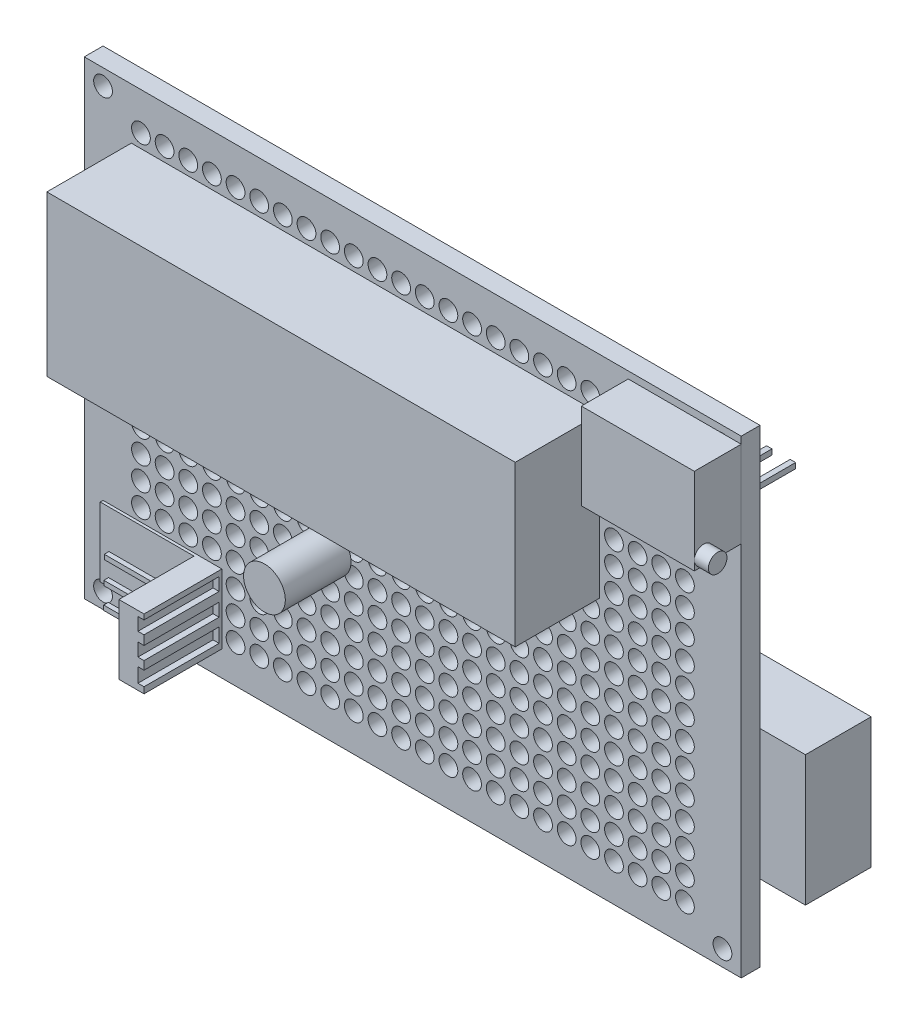
SolidWorks part; units mm, degrees
ref_plane "前视基准面" through (0, 0, 0) normal (0, 0, 1) x (1, 0, 0)
ref_plane "上视基准面" through (0, 0, 0) normal (0, 1, 0) x (1, 0, 0)
ref_plane "右视基准面" through (0, 0, 0) normal (1, 0, 0) x (0, 0, -1)
sketch "草图1" plane through (0, 0, 0) normal (0, 0, 1) x (1, 0, 0)
  line L1 (-36.6719, 23.0469) -> (33.3281, 23.0469)
  line L2 (-36.6719, 23.0469) -> (-36.6719, -26.9531)
  line L3 (-36.6719, -26.9531) -> (33.3281, -26.9531)
  line L4 (33.3281, 23.0469) -> (33.3281, -26.9531)
  circle A0 centre (31.3281, 21.3469) radius 1
  circle A1 centre (-34.6719, -25.2531) radius 1
  circle A2 centre (-34.6719, 21.3469) radius 1
  circle A3 centre (31.3281, -25.2531) radius 1
extrude "凸台-拉伸1" add sketch "草图1" along normal blind 2
sketch "草图2" plane through (0, 0, 0) normal (0, 0, -1) x (-1, 0, 0)
  circle A0 centre (-27.3281, 19.0469) radius 1
  circle A1 centre (-24.8081, 19.0469) radius 1
  circle A2 centre (-22.2881, 19.0469) radius 1
  circle A3 centre (-19.7681, 19.0469) radius 1
  circle A4 centre (-17.2481, 19.0469) radius 1
  circle A5 centre (-14.7281, 19.0469) radius 1
  circle A6 centre (-12.2081, 19.0469) radius 1
  circle A7 centre (-9.6881, 19.0469) radius 1
  circle A8 centre (-7.1681, 19.0469) radius 1
  circle A9 centre (-4.6481, 19.0469) radius 1
  circle A10 centre (-2.1281, 19.0469) radius 1
  circle A11 centre (0.3919, 19.0469) radius 1
  circle A12 centre (2.9119, 19.0469) radius 1
  circle A13 centre (5.4319, 19.0469) radius 1
  circle A14 centre (7.9519, 19.0469) radius 1
  circle A15 centre (10.4719, 19.0469) radius 1
  circle A16 centre (12.9919, 19.0469) radius 1
  circle A17 centre (15.5119, 19.0469) radius 1
  circle A18 centre (18.0319, 19.0469) radius 1
  circle A19 centre (20.5519, 19.0469) radius 1
  circle A20 centre (23.0719, 19.0469) radius 1
  circle A21 centre (25.5919, 19.0469) radius 1
  circle A22 centre (28.1119, 19.0469) radius 1
  circle A23 centre (30.6319, 19.0469) radius 1
  circle A24 centre (-24.8081, 16.5769) radius 1
  circle A25 centre (-22.2881, 16.5769) radius 1
  circle A26 centre (-19.7681, 16.5769) radius 1
  circle A27 centre (-17.2481, 16.5769) radius 1
  circle A28 centre (-14.7281, 16.5769) radius 1
  circle A29 centre (-12.2081, 16.5769) radius 1
  circle A30 centre (-9.6881, 16.5769) radius 1
  circle A31 centre (-7.1681, 16.5769) radius 1
  circle A32 centre (-4.6481, 16.5769) radius 1
  circle A33 centre (-2.1281, 16.5769) radius 1
  circle A34 centre (0.3919, 16.5769) radius 1
  circle A35 centre (2.9119, 16.5769) radius 1
  circle A36 centre (5.4319, 16.5769) radius 1
  circle A37 centre (7.9519, 16.5769) radius 1
  circle A38 centre (10.4719, 16.5769) radius 1
  circle A39 centre (12.9919, 16.5769) radius 1
  circle A40 centre (15.5119, 16.5769) radius 1
  circle A41 centre (18.0319, 16.5769) radius 1
  circle A42 centre (20.5519, 16.5769) radius 1
  circle A43 centre (23.0719, 16.5769) radius 1
  circle A44 centre (25.5919, 16.5769) radius 1
  circle A45 centre (28.1119, 16.5769) radius 1
  circle A46 centre (30.6319, 16.5769) radius 1
  circle A47 centre (-24.8081, 14.1069) radius 1
  circle A48 centre (-22.2881, 14.1069) radius 1
  circle A49 centre (-19.7681, 14.1069) radius 1
  circle A50 centre (-17.2481, 14.1069) radius 1
  circle A51 centre (-14.7281, 14.1069) radius 1
  circle A52 centre (-12.2081, 14.1069) radius 1
  circle A53 centre (-9.6881, 14.1069) radius 1
  circle A54 centre (-7.1681, 14.1069) radius 1
  circle A55 centre (-4.6481, 14.1069) radius 1
  circle A56 centre (-2.1281, 14.1069) radius 1
  circle A57 centre (0.3919, 14.1069) radius 1
  circle A58 centre (2.9119, 14.1069) radius 1
  circle A59 centre (5.4319, 14.1069) radius 1
  circle A60 centre (7.9519, 14.1069) radius 1
  circle A61 centre (10.4719, 14.1069) radius 1
  circle A62 centre (12.9919, 14.1069) radius 1
  circle A63 centre (15.5119, 14.1069) radius 1
  circle A64 centre (18.0319, 14.1069) radius 1
  circle A65 centre (20.5519, 14.1069) radius 1
  circle A66 centre (23.0719, 14.1069) radius 1
  circle A67 centre (25.5919, 14.1069) radius 1
  circle A68 centre (28.1119, 14.1069) radius 1
  circle A69 centre (30.6319, 14.1069) radius 1
  circle A70 centre (-24.8081, 11.6369) radius 1
  circle A71 centre (-22.2881, 11.6369) radius 1
  circle A72 centre (-19.7681, 11.6369) radius 1
  circle A73 centre (-17.2481, 11.6369) radius 1
  circle A74 centre (-14.7281, 11.6369) radius 1
  circle A75 centre (-12.2081, 11.6369) radius 1
  circle A76 centre (-9.6881, 11.6369) radius 1
  circle A77 centre (-7.1681, 11.6369) radius 1
  circle A78 centre (-4.6481, 11.6369) radius 1
  circle A79 centre (-2.1281, 11.6369) radius 1
  circle A80 centre (0.3919, 11.6369) radius 1
  circle A81 centre (2.9119, 11.6369) radius 1
  circle A82 centre (5.4319, 11.6369) radius 1
  circle A83 centre (7.9519, 11.6369) radius 1
  circle A84 centre (10.4719, 11.6369) radius 1
  circle A85 centre (12.9919, 11.6369) radius 1
  circle A86 centre (15.5119, 11.6369) radius 1
  circle A87 centre (18.0319, 11.6369) radius 1
  circle A88 centre (20.5519, 11.6369) radius 1
  circle A89 centre (23.0719, 11.6369) radius 1
  circle A90 centre (25.5919, 11.6369) radius 1
  circle A91 centre (28.1119, 11.6369) radius 1
  circle A92 centre (30.6319, 11.6369) radius 1
  circle A93 centre (-24.8081, 9.1669) radius 1
  circle A94 centre (-22.2881, 9.1669) radius 1
  circle A95 centre (-19.7681, 9.1669) radius 1
  circle A96 centre (-17.2481, 9.1669) radius 1
  circle A97 centre (-14.7281, 9.1669) radius 1
  circle A98 centre (-12.2081, 9.1669) radius 1
  circle A99 centre (-9.6881, 9.1669) radius 1
  circle A100 centre (-7.1681, 9.1669) radius 1
  circle A101 centre (-4.6481, 9.1669) radius 1
  circle A102 centre (-2.1281, 9.1669) radius 1
  circle A103 centre (0.3919, 9.1669) radius 1
  circle A104 centre (2.9119, 9.1669) radius 1
  circle A105 centre (5.4319, 9.1669) radius 1
  circle A106 centre (7.9519, 9.1669) radius 1
  circle A107 centre (10.4719, 9.1669) radius 1
  circle A108 centre (12.9919, 9.1669) radius 1
  circle A109 centre (15.5119, 9.1669) radius 1
  circle A110 centre (18.0319, 9.1669) radius 1
  circle A111 centre (20.5519, 9.1669) radius 1
  circle A112 centre (23.0719, 9.1669) radius 1
  circle A113 centre (25.5919, 9.1669) radius 1
  circle A114 centre (28.1119, 9.1669) radius 1
  circle A115 centre (30.6319, 9.1669) radius 1
  circle A116 centre (-24.8081, 6.6969) radius 1
  circle A117 centre (-22.2881, 6.6969) radius 1
  circle A118 centre (-19.7681, 6.6969) radius 1
  circle A119 centre (-17.2481, 6.6969) radius 1
  circle A120 centre (-14.7281, 6.6969) radius 1
  circle A121 centre (-12.2081, 6.6969) radius 1
  circle A122 centre (-9.6881, 6.6969) radius 1
  circle A123 centre (-7.1681, 6.6969) radius 1
  circle A124 centre (-4.6481, 6.6969) radius 1
  circle A125 centre (-2.1281, 6.6969) radius 1
  circle A126 centre (0.3919, 6.6969) radius 1
  circle A127 centre (2.9119, 6.6969) radius 1
  circle A128 centre (5.4319, 6.6969) radius 1
  circle A129 centre (7.9519, 6.6969) radius 1
  circle A130 centre (10.4719, 6.6969) radius 1
  circle A131 centre (12.9919, 6.6969) radius 1
  circle A132 centre (15.5119, 6.6969) radius 1
  circle A133 centre (18.0319, 6.6969) radius 1
  circle A134 centre (20.5519, 6.6969) radius 1
  circle A135 centre (23.0719, 6.6969) radius 1
  circle A136 centre (25.5919, 6.6969) radius 1
  circle A137 centre (28.1119, 6.6969) radius 1
  circle A138 centre (30.6319, 6.6969) radius 1
  circle A139 centre (-24.8081, 4.2269) radius 1
  circle A140 centre (-22.2881, 4.2269) radius 1
  circle A141 centre (-19.7681, 4.2269) radius 1
  circle A142 centre (-17.2481, 4.2269) radius 1
  circle A143 centre (-14.7281, 4.2269) radius 1
  circle A144 centre (-12.2081, 4.2269) radius 1
  circle A145 centre (-9.6881, 4.2269) radius 1
  circle A146 centre (-7.1681, 4.2269) radius 1
  circle A147 centre (-4.6481, 4.2269) radius 1
  circle A148 centre (-2.1281, 4.2269) radius 1
  circle A149 centre (0.3919, 4.2269) radius 1
  circle A150 centre (2.9119, 4.2269) radius 1
  circle A151 centre (5.4319, 4.2269) radius 1
  circle A152 centre (7.9519, 4.2269) radius 1
  circle A153 centre (10.4719, 4.2269) radius 1
  circle A154 centre (12.9919, 4.2269) radius 1
  circle A155 centre (15.5119, 4.2269) radius 1
  circle A156 centre (18.0319, 4.2269) radius 1
  circle A157 centre (20.5519, 4.2269) radius 1
  circle A158 centre (23.0719, 4.2269) radius 1
  circle A159 centre (25.5919, 4.2269) radius 1
  circle A160 centre (28.1119, 4.2269) radius 1
  circle A161 centre (30.6319, 4.2269) radius 1
  circle A162 centre (-24.8081, 1.7569) radius 1
  circle A163 centre (-22.2881, 1.7569) radius 1
  circle A164 centre (-19.7681, 1.7569) radius 1
  circle A165 centre (-17.2481, 1.7569) radius 1
  circle A166 centre (-14.7281, 1.7569) radius 1
  circle A167 centre (-12.2081, 1.7569) radius 1
  circle A168 centre (-9.6881, 1.7569) radius 1
  circle A169 centre (-7.1681, 1.7569) radius 1
  circle A170 centre (-4.6481, 1.7569) radius 1
  circle A171 centre (-2.1281, 1.7569) radius 1
  circle A172 centre (0.3919, 1.7569) radius 1
  circle A173 centre (2.9119, 1.7569) radius 1
  circle A174 centre (5.4319, 1.7569) radius 1
  circle A175 centre (7.9519, 1.7569) radius 1
  circle A176 centre (10.4719, 1.7569) radius 1
  circle A177 centre (12.9919, 1.7569) radius 1
  circle A178 centre (15.5119, 1.7569) radius 1
  circle A179 centre (18.0319, 1.7569) radius 1
  circle A180 centre (20.5519, 1.7569) radius 1
  circle A181 centre (23.0719, 1.7569) radius 1
  circle A182 centre (25.5919, 1.7569) radius 1
  circle A183 centre (28.1119, 1.7569) radius 1
  circle A184 centre (30.6319, 1.7569) radius 1
  circle A185 centre (-24.8081, -0.7131) radius 1
  circle A186 centre (-22.2881, -0.7131) radius 1
  circle A187 centre (-19.7681, -0.7131) radius 1
  circle A188 centre (-17.2481, -0.7131) radius 1
  circle A189 centre (-14.7281, -0.7131) radius 1
  circle A190 centre (-12.2081, -0.7131) radius 1
  circle A191 centre (-9.6881, -0.7131) radius 1
  circle A192 centre (-7.1681, -0.7131) radius 1
  circle A193 centre (-4.6481, -0.7131) radius 1
  circle A194 centre (-2.1281, -0.7131) radius 1
  circle A195 centre (0.3919, -0.7131) radius 1
  circle A196 centre (2.9119, -0.7131) radius 1
  circle A197 centre (5.4319, -0.7131) radius 1
  circle A198 centre (7.9519, -0.7131) radius 1
  circle A199 centre (10.4719, -0.7131) radius 1
  circle A200 centre (12.9919, -0.7131) radius 1
  circle A201 centre (15.5119, -0.7131) radius 1
  circle A202 centre (18.0319, -0.7131) radius 1
  circle A203 centre (20.5519, -0.7131) radius 1
  circle A204 centre (23.0719, -0.7131) radius 1
  circle A205 centre (25.5919, -0.7131) radius 1
  circle A206 centre (28.1119, -0.7131) radius 1
  circle A207 centre (30.6319, -0.7131) radius 1
  circle A208 centre (-24.8081, -3.1831) radius 1
  circle A209 centre (-22.2881, -3.1831) radius 1
  circle A210 centre (-19.7681, -3.1831) radius 1
  circle A211 centre (-17.2481, -3.1831) radius 1
  circle A212 centre (-14.7281, -3.1831) radius 1
  circle A213 centre (-12.2081, -3.1831) radius 1
  circle A214 centre (-9.6881, -3.1831) radius 1
  circle A215 centre (-7.1681, -3.1831) radius 1
  circle A216 centre (-4.6481, -3.1831) radius 1
  circle A217 centre (-2.1281, -3.1831) radius 1
  circle A218 centre (0.3919, -3.1831) radius 1
  circle A219 centre (2.9119, -3.1831) radius 1
  circle A220 centre (5.4319, -3.1831) radius 1
  circle A221 centre (7.9519, -3.1831) radius 1
  circle A222 centre (10.4719, -3.1831) radius 1
  circle A223 centre (12.9919, -3.1831) radius 1
  circle A224 centre (15.5119, -3.1831) radius 1
  circle A225 centre (18.0319, -3.1831) radius 1
  circle A226 centre (20.5519, -3.1831) radius 1
  circle A227 centre (23.0719, -3.1831) radius 1
  circle A228 centre (25.5919, -3.1831) radius 1
  circle A229 centre (28.1119, -3.1831) radius 1
  circle A230 centre (30.6319, -3.1831) radius 1
  circle A231 centre (-24.8081, -5.6531) radius 1
  circle A232 centre (-22.2881, -5.6531) radius 1
  circle A233 centre (-19.7681, -5.6531) radius 1
  circle A234 centre (-17.2481, -5.6531) radius 1
  circle A235 centre (-14.7281, -5.6531) radius 1
  circle A236 centre (-12.2081, -5.6531) radius 1
  circle A237 centre (-9.6881, -5.6531) radius 1
  circle A238 centre (-7.1681, -5.6531) radius 1
  circle A239 centre (-4.6481, -5.6531) radius 1
  circle A240 centre (-2.1281, -5.6531) radius 1
  circle A241 centre (0.3919, -5.6531) radius 1
  circle A242 centre (2.9119, -5.6531) radius 1
  circle A243 centre (5.4319, -5.6531) radius 1
  circle A244 centre (7.9519, -5.6531) radius 1
  circle A245 centre (10.4719, -5.6531) radius 1
  circle A246 centre (12.9919, -5.6531) radius 1
  circle A247 centre (15.5119, -5.6531) radius 1
  circle A248 centre (18.0319, -5.6531) radius 1
  circle A249 centre (20.5519, -5.6531) radius 1
  circle A250 centre (23.0719, -5.6531) radius 1
  circle A251 centre (25.5919, -5.6531) radius 1
  circle A252 centre (28.1119, -5.6531) radius 1
  circle A253 centre (30.6319, -5.6531) radius 1
  circle A254 centre (-24.8081, -8.1231) radius 1
  circle A255 centre (-22.2881, -8.1231) radius 1
  circle A256 centre (-19.7681, -8.1231) radius 1
  circle A257 centre (-17.2481, -8.1231) radius 1
  circle A258 centre (-14.7281, -8.1231) radius 1
  circle A259 centre (-12.2081, -8.1231) radius 1
  circle A260 centre (-9.6881, -8.1231) radius 1
  circle A261 centre (-7.1681, -8.1231) radius 1
  circle A262 centre (-4.6481, -8.1231) radius 1
  circle A263 centre (-2.1281, -8.1231) radius 1
  circle A264 centre (0.3919, -8.1231) radius 1
  circle A265 centre (2.9119, -8.1231) radius 1
  circle A266 centre (5.4319, -8.1231) radius 1
  circle A267 centre (7.9519, -8.1231) radius 1
  circle A268 centre (10.4719, -8.1231) radius 1
  circle A269 centre (12.9919, -8.1231) radius 1
  circle A270 centre (15.5119, -8.1231) radius 1
  circle A271 centre (18.0319, -8.1231) radius 1
  circle A272 centre (20.5519, -8.1231) radius 1
  circle A273 centre (23.0719, -8.1231) radius 1
  circle A274 centre (25.5919, -8.1231) radius 1
  circle A275 centre (28.1119, -8.1231) radius 1
  circle A276 centre (30.6319, -8.1231) radius 1
  circle A277 centre (-24.8081, -10.5931) radius 1
  circle A278 centre (-22.2881, -10.5931) radius 1
  circle A279 centre (-19.7681, -10.5931) radius 1
  circle A280 centre (-17.2481, -10.5931) radius 1
  circle A281 centre (-14.7281, -10.5931) radius 1
  circle A282 centre (-12.2081, -10.5931) radius 1
  circle A283 centre (-9.6881, -10.5931) radius 1
  circle A284 centre (-7.1681, -10.5931) radius 1
  circle A285 centre (-4.6481, -10.5931) radius 1
  circle A286 centre (-2.1281, -10.5931) radius 1
  circle A287 centre (0.3919, -10.5931) radius 1
  circle A288 centre (2.9119, -10.5931) radius 1
  circle A289 centre (5.4319, -10.5931) radius 1
  circle A290 centre (7.9519, -10.5931) radius 1
  circle A291 centre (10.4719, -10.5931) radius 1
  circle A292 centre (12.9919, -10.5931) radius 1
  circle A293 centre (15.5119, -10.5931) radius 1
  circle A294 centre (18.0319, -10.5931) radius 1
  circle A295 centre (20.5519, -10.5931) radius 1
  circle A296 centre (23.0719, -10.5931) radius 1
  circle A297 centre (25.5919, -10.5931) radius 1
  circle A298 centre (28.1119, -10.5931) radius 1
  circle A299 centre (30.6319, -10.5931) radius 1
  circle A300 centre (-24.8081, -13.0631) radius 1
  circle A301 centre (-22.2881, -13.0631) radius 1
  circle A302 centre (-19.7681, -13.0631) radius 1
  circle A303 centre (-17.2481, -13.0631) radius 1
  circle A304 centre (-14.7281, -13.0631) radius 1
  circle A305 centre (-12.2081, -13.0631) radius 1
  circle A306 centre (-9.6881, -13.0631) radius 1
  circle A307 centre (-7.1681, -13.0631) radius 1
  circle A308 centre (-4.6481, -13.0631) radius 1
  circle A309 centre (-2.1281, -13.0631) radius 1
  circle A310 centre (0.3919, -13.0631) radius 1
  circle A311 centre (2.9119, -13.0631) radius 1
  circle A312 centre (5.4319, -13.0631) radius 1
  circle A313 centre (7.9519, -13.0631) radius 1
  circle A314 centre (10.4719, -13.0631) radius 1
  circle A315 centre (12.9919, -13.0631) radius 1
  circle A316 centre (15.5119, -13.0631) radius 1
  circle A317 centre (18.0319, -13.0631) radius 1
  circle A318 centre (20.5519, -13.0631) radius 1
  circle A319 centre (23.0719, -13.0631) radius 1
  circle A320 centre (25.5919, -13.0631) radius 1
  circle A321 centre (28.1119, -13.0631) radius 1
  circle A322 centre (30.6319, -13.0631) radius 1
  circle A323 centre (-24.8081, -15.5331) radius 1
  circle A324 centre (-22.2881, -15.5331) radius 1
  circle A325 centre (-19.7681, -15.5331) radius 1
  circle A326 centre (-17.2481, -15.5331) radius 1
  circle A327 centre (-14.7281, -15.5331) radius 1
  circle A328 centre (-12.2081, -15.5331) radius 1
  circle A329 centre (-9.6881, -15.5331) radius 1
  circle A330 centre (-7.1681, -15.5331) radius 1
  circle A331 centre (-4.6481, -15.5331) radius 1
  circle A332 centre (-2.1281, -15.5331) radius 1
  circle A333 centre (0.3919, -15.5331) radius 1
  circle A334 centre (2.9119, -15.5331) radius 1
  circle A335 centre (5.4319, -15.5331) radius 1
  circle A336 centre (7.9519, -15.5331) radius 1
  circle A337 centre (10.4719, -15.5331) radius 1
  circle A338 centre (12.9919, -15.5331) radius 1
  circle A339 centre (15.5119, -15.5331) radius 1
  circle A340 centre (18.0319, -15.5331) radius 1
  circle A341 centre (20.5519, -15.5331) radius 1
  circle A342 centre (23.0719, -15.5331) radius 1
  circle A343 centre (25.5919, -15.5331) radius 1
  circle A344 centre (28.1119, -15.5331) radius 1
  circle A345 centre (30.6319, -15.5331) radius 1
  circle A346 centre (-24.8081, -18.0031) radius 1
  circle A347 centre (-22.2881, -18.0031) radius 1
  circle A348 centre (-19.7681, -18.0031) radius 1
  circle A349 centre (-17.2481, -18.0031) radius 1
  circle A350 centre (-14.7281, -18.0031) radius 1
  circle A351 centre (-12.2081, -18.0031) radius 1
  circle A352 centre (-9.6881, -18.0031) radius 1
  circle A353 centre (-7.1681, -18.0031) radius 1
  circle A354 centre (-4.6481, -18.0031) radius 1
  circle A355 centre (-2.1281, -18.0031) radius 1
  circle A356 centre (0.3919, -18.0031) radius 1
  circle A357 centre (2.9119, -18.0031) radius 1
  circle A358 centre (5.4319, -18.0031) radius 1
  circle A359 centre (7.9519, -18.0031) radius 1
  circle A360 centre (10.4719, -18.0031) radius 1
  circle A361 centre (12.9919, -18.0031) radius 1
  circle A362 centre (15.5119, -18.0031) radius 1
  circle A363 centre (18.0319, -18.0031) radius 1
  circle A364 centre (20.5519, -18.0031) radius 1
  circle A365 centre (23.0719, -18.0031) radius 1
  circle A366 centre (25.5919, -18.0031) radius 1
  circle A367 centre (28.1119, -18.0031) radius 1
  circle A368 centre (30.6319, -18.0031) radius 1
  circle A369 centre (-24.8081, -20.4731) radius 1
  circle A370 centre (-22.2881, -20.4731) radius 1
  circle A371 centre (-19.7681, -20.4731) radius 1
  circle A372 centre (-17.2481, -20.4731) radius 1
  circle A373 centre (-14.7281, -20.4731) radius 1
  circle A374 centre (-12.2081, -20.4731) radius 1
  circle A375 centre (-9.6881, -20.4731) radius 1
  circle A376 centre (-7.1681, -20.4731) radius 1
  circle A377 centre (-4.6481, -20.4731) radius 1
  circle A378 centre (-2.1281, -20.4731) radius 1
  circle A379 centre (0.3919, -20.4731) radius 1
  circle A380 centre (2.9119, -20.4731) radius 1
  circle A381 centre (5.4319, -20.4731) radius 1
  circle A382 centre (7.9519, -20.4731) radius 1
  circle A383 centre (10.4719, -20.4731) radius 1
  circle A384 centre (12.9919, -20.4731) radius 1
  circle A385 centre (15.5119, -20.4731) radius 1
  circle A386 centre (18.0319, -20.4731) radius 1
  circle A387 centre (20.5519, -20.4731) radius 1
  circle A388 centre (23.0719, -20.4731) radius 1
  circle A389 centre (25.5919, -20.4731) radius 1
  circle A390 centre (28.1119, -20.4731) radius 1
  circle A391 centre (30.6319, -20.4731) radius 1
  circle A392 centre (-24.8081, -22.9431) radius 1
  circle A393 centre (-22.2881, -22.9431) radius 1
  circle A394 centre (-19.7681, -22.9431) radius 1
  circle A395 centre (-17.2481, -22.9431) radius 1
  circle A396 centre (-14.7281, -22.9431) radius 1
  circle A397 centre (-12.2081, -22.9431) radius 1
  circle A398 centre (-9.6881, -22.9431) radius 1
  circle A399 centre (-7.1681, -22.9431) radius 1
  circle A400 centre (-4.6481, -22.9431) radius 1
  circle A401 centre (-2.1281, -22.9431) radius 1
  circle A402 centre (0.3919, -22.9431) radius 1
  circle A403 centre (2.9119, -22.9431) radius 1
  circle A404 centre (5.4319, -22.9431) radius 1
  circle A405 centre (7.9519, -22.9431) radius 1
  circle A406 centre (10.4719, -22.9431) radius 1
  circle A407 centre (12.9919, -22.9431) radius 1
  circle A408 centre (15.5119, -22.9431) radius 1
  circle A409 centre (18.0319, -22.9431) radius 1
  circle A410 centre (20.5519, -22.9431) radius 1
  circle A411 centre (23.0719, -22.9431) radius 1
  circle A412 centre (25.5919, -22.9431) radius 1
  circle A413 centre (28.1119, -22.9431) radius 1
  circle A414 centre (30.6319, -22.9431) radius 1
  circle A415 centre (-27.3281, 16.5769) radius 1
  circle A416 centre (-27.3281, 14.1069) radius 1
  circle A417 centre (-27.3281, 11.6369) radius 1
  circle A418 centre (-27.3281, 9.1669) radius 1
  circle A419 centre (-27.3281, 6.6969) radius 1
  circle A420 centre (-27.3281, 4.2269) radius 1
  circle A421 centre (-27.3281, 1.7569) radius 1
  circle A422 centre (-27.3281, -0.7131) radius 1
  circle A423 centre (-27.3281, -3.1831) radius 1
  circle A424 centre (-27.3281, -5.6531) radius 1
  circle A425 centre (-27.3281, -8.1231) radius 1
  circle A426 centre (-27.3281, -10.5931) radius 1
  circle A427 centre (-27.3281, -13.0631) radius 1
  circle A428 centre (-27.3281, -15.5331) radius 1
  circle A429 centre (-27.3281, -18.0031) radius 1
  circle A430 centre (-27.3281, -20.4731) radius 1
  circle A431 centre (-27.3281, -22.9431) radius 1
  dimension "D1" = 24
  dimension "D2" = 18
extrude "切除-拉伸1" cut sketch "草图2" against normal blind 2
sketch "草图3" plane through (0, 0, 2) normal (0, 0, 1) x (1, 0, 0)
  line L1 (-31.656, 17.5923) -> (18.2481, 17.5923)
  line L2 (-31.656, 17.5923) -> (-31.656, 0.5632)
  line L3 (-31.656, 0.5632) -> (18.2481, 0.5632)
  line L4 (18.2481, 17.5923) -> (18.2481, 0.5632)
extrude "凸台-拉伸3" add sketch "草图3" along normal blind 9 separate body
sketch "草图4" plane through (0, 0, 2) normal (0, 0, 1) x (1, 0, 0)
  line L0 (33.3281, -26.9531) -> (33.3281, 23.0469) construction
  line L1 (33.3281, 22.3025) -> (21.2881, 22.3025)
  line L2 (33.3281, 22.3025) -> (33.3281, 13.1069)
  line L3 (33.3281, 13.1069) -> (21.2881, 13.1069)
  line L4 (21.2881, 22.3025) -> (21.2881, 13.1069)
extrude "凸台-拉伸4" add sketch "草图4" along normal blind 5 separate body
sketch "草图5" plane through (33.3281, 0, 0) normal (1, 0, 0) x (0, 0, -1)
  circle A0 centre (-6.0085, 14.0984) radius 0.9915
extrude "凸台-拉伸5" add sketch "草图5" along normal blind 1.5
sketch "草图6" plane through (0, 0, 2) normal (0, 0, 1) x (1, 0, 0)
  line L1 (-34.6719, -24.2531) -> (-22.0048, -24.2531)
  line L2 (-34.6719, -24.2531) -> (-34.6719, -16.8774)
  line L3 (-34.6719, -16.8774) -> (-22.0048, -16.8774)
  line L4 (-22.0048, -24.2531) -> (-22.0048, -16.8774)
  circle A0 centre (-34.6719, -25.2531) radius 1 construction
extrude "凸台-拉伸6" add sketch "草图6" along normal blind 0.3
sketch "草图7" plane through (0, 0, 2.3) normal (0, 0, 1) x (1, 0, 0)
  line L1 (-22.0048, -16.8774) -> (-34.6719, -16.8774) construction
  line L2 (-34.6719, -24.2531) -> (-22.0048, -24.2531) construction
  line L3 (-24.6793, -24.2531) -> (-22.0048, -24.2531)
  line L4 (-22.0048, -16.8774) -> (-22.0048, -17.4292)
  line L5 (-22.0048, -24.2531) -> (-22.0048, -16.8774) construction
  line L6 (-22.0048, -24.2531) -> (-22.0048, -16.8774) construction
  line L7 (-22.0048, -17.4292) -> (-22.6503, -17.4292)
  line L8 (-22.6503, -17.4292) -> (-22.6503, -18.8012)
  line L9 (-22.6503, -18.8012) -> (-22.0048, -18.8012)
  line L10 (-22.0048, -18.8012) -> (-22.0048, -19.7867)
  line L11 (-22.0048, -19.7867) -> (-22.6503, -19.7867)
  line L12 (-22.6503, -19.7867) -> (-22.6503, -21.1781)
  line L13 (-22.6503, -21.1781) -> (-22.0048, -21.1781)
  line L14 (-22.0048, -21.1781) -> (-22.0048, -22.067)
  line L15 (-22.0048, -22.067) -> (-22.6503, -22.067)
  line L16 (-22.6503, -22.067) -> (-22.6503, -23.5936)
  line L17 (-22.6503, -23.5936) -> (-22.0048, -23.5936)
  line L18 (-22.0048, -23.5936) -> (-22.0048, -24.2531)
  line L19 (-24.6793, -24.2531) -> (-24.6793, -16.8774)
  line L20 (-22.0048, -16.8774) -> (-24.6793, -16.8774)
extrude "凸台-拉伸7" add sketch "草图7" along normal blind 8
sketch "草图8" plane through (-22.6503, 0, 0) normal (1, 0, 0) x (0, 0, -1)
  line L0 (-5.9346, -20.2759) -> (-5.4346, -20.2759)
  line L1 (-5.8878, -17.8955) -> (-5.3878, -17.8955)
  line L2 (-5.8878, -17.8955) -> (-5.8878, -18.3955)
  line L3 (-5.8878, -18.3955) -> (-5.3878, -18.3955)
  line L4 (-5.3878, -17.8955) -> (-5.3878, -18.3955)
  line L5 (-5.9346, -20.2759) -> (-5.9346, -20.7759)
  line L6 (-5.9346, -20.7759) -> (-5.4346, -20.7759)
  line L7 (-5.4346, -20.2759) -> (-5.4346, -20.7759)
  line L8 (-5.9491, -22.5548) -> (-5.4491, -22.5548)
  line L9 (-5.9491, -22.5548) -> (-5.9491, -23.0548)
  line L10 (-5.9491, -23.0548) -> (-5.4491, -23.0548)
  line L11 (-5.4491, -22.5548) -> (-5.4491, -23.0548)
extrude "凸台-拉伸8" add sketch "草图8" against normal blind 8
sketch "草图9" plane through (0, 0, 2) normal (0, 0, 1) x (1, 0, 0)
  circle A1 centre (-10.4719, -9.3623) radius 2.2236
extrude "凸台-拉伸9" add sketch "草图9" along normal blind 7
sketch "草图10" plane through (0, 0, 0) normal (0, 0, -1) x (-1, 0, 0)
  line L1 (-38.1694, -4.9279) -> (-24.0487, -4.9279)
  line L2 (-38.1694, -4.9279) -> (-38.1694, -18.8132)
  line L3 (-38.1694, -18.8132) -> (-24.0487, -18.8132)
  line L4 (-24.0487, -4.9279) -> (-24.0487, -18.8132)
extrude "凸台-拉伸12" add sketch "草图10" along normal blind 7 separate body
sketch "草图12" plane through (0, 0, 0) normal (0, 0, -1) x (-1, 0, 0)
  line L1 (6.7255, 10.4406) -> (-28.7236, 10.4406)
  line L2 (6.7255, 10.4406) -> (6.7255, 12.9106)
  line L3 (6.7255, 12.9106) -> (-28.7236, 12.9106)
  line L4 (-28.7236, 10.4406) -> (-28.7236, 12.9106)
extrude "凸台-拉伸13" add sketch "草图12" along normal blind 2.5
sketch "草图13" plane through (0, 0, -2.5) normal (0, 0, -1) x (-1, 0, 0)
  line L0 (3.1925, 12.0124) -> (2.6154, 12.0124)
  line L1 (5.7125, 12.0124) -> (5.1354, 12.0124)
  line L2 (5.7125, 12.0124) -> (5.7125, 11.4352)
  line L3 (5.7125, 11.4352) -> (5.1354, 11.4352)
  line L4 (5.1354, 12.0124) -> (5.1354, 11.4352)
  line L5 (3.1925, 12.0124) -> (3.1925, 11.4352)
  line L6 (3.1925, 11.4352) -> (2.6154, 11.4352)
  line L7 (2.6154, 12.0124) -> (2.6154, 11.4352)
  line L8 (0.6725, 12.0124) -> (0.0954, 12.0124)
  line L9 (0.6725, 12.0124) -> (0.6725, 11.4352)
  line L10 (0.6725, 11.4352) -> (0.0954, 11.4352)
  line L11 (0.0954, 12.0124) -> (0.0954, 11.4352)
  line L12 (-1.8475, 12.0124) -> (-2.4246, 12.0124)
  line L13 (-1.8475, 12.0124) -> (-1.8475, 11.4352)
  line L14 (-1.8475, 11.4352) -> (-2.4246, 11.4352)
  line L15 (-2.4246, 12.0124) -> (-2.4246, 11.4352)
  line L16 (-4.3675, 12.0124) -> (-4.9446, 12.0124)
  line L17 (-4.3675, 12.0124) -> (-4.3675, 11.4352)
  line L18 (-4.3675, 11.4352) -> (-4.9446, 11.4352)
  line L19 (-4.9446, 12.0124) -> (-4.9446, 11.4352)
  line L20 (-6.8875, 12.0124) -> (-7.4646, 12.0124)
  line L21 (-6.8875, 12.0124) -> (-6.8875, 11.4352)
  line L22 (-6.8875, 11.4352) -> (-7.4646, 11.4352)
  line L23 (-7.4646, 12.0124) -> (-7.4646, 11.4352)
  line L24 (-9.4075, 12.0124) -> (-9.9846, 12.0124)
  line L25 (-9.4075, 12.0124) -> (-9.4075, 11.4352)
  line L26 (-9.4075, 11.4352) -> (-9.9846, 11.4352)
  line L27 (-9.9846, 12.0124) -> (-9.9846, 11.4352)
  line L28 (-11.9275, 12.0124) -> (-12.5046, 12.0124)
  line L29 (-11.9275, 12.0124) -> (-11.9275, 11.4352)
  line L30 (-11.9275, 11.4352) -> (-12.5046, 11.4352)
  line L31 (-12.5046, 12.0124) -> (-12.5046, 11.4352)
  line L32 (-14.4475, 12.0124) -> (-15.0246, 12.0124)
  line L33 (-14.4475, 12.0124) -> (-14.4475, 11.4352)
  line L34 (-14.4475, 11.4352) -> (-15.0246, 11.4352)
  line L35 (-15.0246, 12.0124) -> (-15.0246, 11.4352)
  line L36 (-16.9675, 12.0124) -> (-17.5446, 12.0124)
  line L37 (-16.9675, 12.0124) -> (-16.9675, 11.4352)
  line L38 (-16.9675, 11.4352) -> (-17.5446, 11.4352)
  line L39 (-17.5446, 12.0124) -> (-17.5446, 11.4352)
  line L40 (-19.4875, 12.0124) -> (-20.0646, 12.0124)
  line L41 (-19.4875, 12.0124) -> (-19.4875, 11.4352)
  line L42 (-19.4875, 11.4352) -> (-20.0646, 11.4352)
  line L43 (-20.0646, 12.0124) -> (-20.0646, 11.4352)
  line L44 (-22.0075, 12.0124) -> (-22.5846, 12.0124)
  line L45 (-22.0075, 12.0124) -> (-22.0075, 11.4352)
  line L46 (-22.0075, 11.4352) -> (-22.5846, 11.4352)
  line L47 (-22.5846, 12.0124) -> (-22.5846, 11.4352)
  line L48 (-24.5275, 12.0124) -> (-25.1046, 12.0124)
  line L49 (-24.5275, 12.0124) -> (-24.5275, 11.4352)
  line L50 (-24.5275, 11.4352) -> (-25.1046, 11.4352)
  line L51 (-25.1046, 12.0124) -> (-25.1046, 11.4352)
  line L52 (-27.0475, 12.0124) -> (-27.6246, 12.0124)
  line L53 (-27.0475, 12.0124) -> (-27.0475, 11.4352)
  line L54 (-27.0475, 11.4352) -> (-27.6246, 11.4352)
  line L55 (-27.6246, 12.0124) -> (-27.6246, 11.4352)
  dimension "D1" = 14
extrude "凸台-拉伸14" add sketch "草图13" along normal blind 7
sketch "草图14" plane through (-0.0784, 0.0588, 0) normal (0, 0, -1) x (-1, 0, 0)
  line L1 (4.0895, -19.4476) -> (-5.9648, -19.4476)
  line L2 (4.0895, -19.4476) -> (4.0895, -21.5944)
  line L3 (4.0895, -21.5944) -> (-5.9648, -21.5944)
  line L4 (-5.9648, -19.4476) -> (-5.9648, -21.5944)
extrude "凸台-拉伸15" add sketch "草图14" along normal blind 2
sketch "草图15" plane through (5.0108, -37.0619, -2) normal (0, 0, -1) x (-1, 0, 0)
  line L0 (2.6818, 16.835) -> (2.6818, 16.3859)
  line L1 (0.1618, 16.835) -> (0.611, 16.835)
  line L2 (0.1618, 16.835) -> (0.1618, 16.3859)
  line L3 (0.1618, 16.3859) -> (0.611, 16.3859)
  line L4 (0.611, 16.835) -> (0.611, 16.3859)
  line L5 (3.131, 16.835) -> (3.131, 16.3859)
  line L6 (2.6818, 16.3859) -> (3.131, 16.3859)
  line L7 (2.6818, 16.835) -> (3.131, 16.835)
  line L8 (5.2018, 16.835) -> (5.2018, 16.3859)
  line L9 (5.651, 16.835) -> (5.651, 16.3859)
  line L10 (5.2018, 16.3859) -> (5.651, 16.3859)
  line L11 (5.2018, 16.835) -> (5.651, 16.835)
  line L12 (7.7218, 16.835) -> (7.7218, 16.3859)
  line L13 (8.171, 16.835) -> (8.171, 16.3859)
  line L14 (7.7218, 16.3859) -> (8.171, 16.3859)
  line L15 (7.7218, 16.835) -> (8.171, 16.835)
  dimension "D1" = 4
extrude "凸台-拉伸17" add sketch "草图15" along normal blind 7
sketch "草图17" plane through (0, 0, 0) normal (0, 0, -1) x (-1, 0, 0)
  line L1 (33.3556, -24.1309) -> (28.0855, -24.1309)
  line L2 (33.3556, -24.1309) -> (33.3556, -20.3344)
  line L3 (33.3556, -20.3344) -> (28.0855, -20.3344)
  line L4 (28.0855, -24.1309) -> (28.0855, -20.3344)
extrude "凸台-拉伸18" add sketch "草图17" along normal blind 2
sketch "草图18" plane through (0, 0, -2) normal (0, 0, -1) x (-1, 0, 0)
  line L1 (29.4374, -21.2097) -> (31.8614, -21.2097)
  line L3 (29.4374, -23.2828) -> (31.8614, -23.2828)
  arc A1 (31.8614, -23.2828) -> (31.8614, -21.2097) centre (31.8614, -22.2463) ccw
  arc A3 (29.4374, -21.2097) -> (29.4374, -23.2828) centre (29.4374, -22.2463) ccw
extrude "凸台-拉伸19" add sketch "草图18" along normal blind 1
